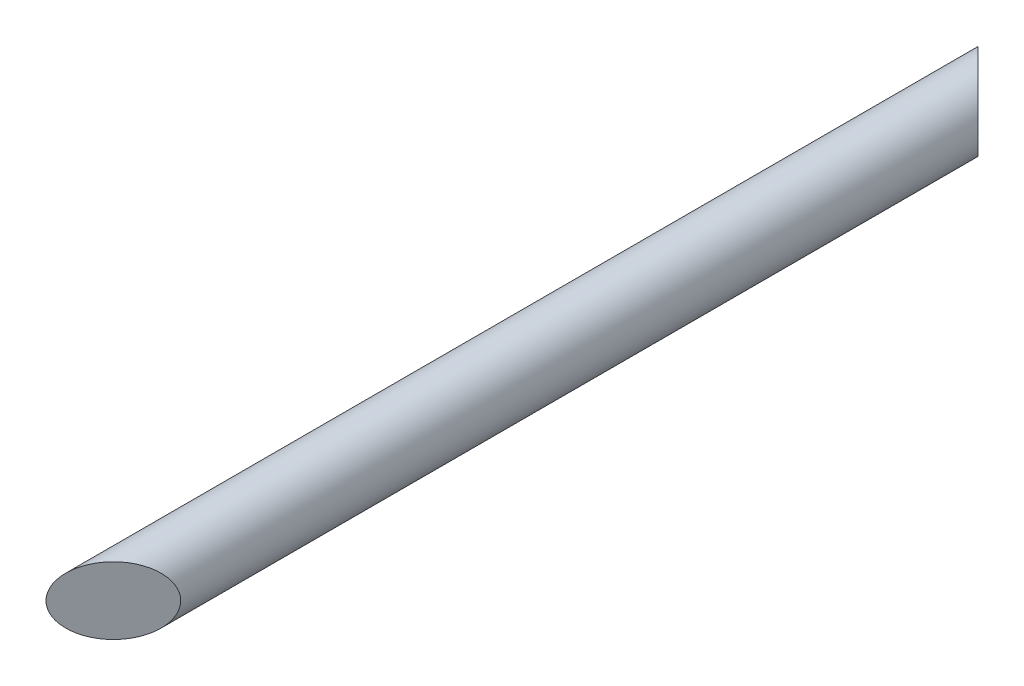
SolidWorks part; units mm, degrees
ref_plane "Front Plane" through (0, 0, 0) normal (0, 0, 1) x (1, 0, 0)
ref_plane "Top Plane" through (0, 0, 0) normal (0, 1, 0) x (1, 0, 0)
ref_plane "Right Plane" through (0, 0, 0) normal (1, 0, 0) x (0, 0, -1)
sketch "Sketch1" plane through (0, 0, 0) normal (0, 0, 1) x (1, 0, 0)
  circle A0 centre (0, 0) radius 30
  dimension "D1" = 60
extrude "Boss-Extrude2" add sketch "Sketch1" along normal blind 830 contours A0
ref_plane "Plane1" through (0, 40, 0) normal (0, 1, 0) x (1, 0, 0)
sketch "Sketch3" plane through (0, 40, 0) normal (0, 1, 0) x (1, 0, 0)
  line L0 (-30, 0) -> (30, -60)
  line L1 (30, -830) -> (30, 0) construction
  line L2 (30, -60) -> (30, 0)
  line L3 (30, 0) -> (-30, 0)
  dimension "D1" = 60
  dimension "D2" = 60
sketch "Sketch4" plane through (0, 40, 0) normal (0, 1, 0) x (1, 0, 0)
  line L0 (-30, -830) -> (30, -830)
  line L1 (30, -830) -> (30, -770)
  line L2 (30, -830) -> (30, 0) construction
  line L3 (30, -770) -> (-30, -830)
  point P4 (39.9956, -792.8601)
  dimension "D1" = 60
extrude "Cut-Extrude4" cut sketch "Sketch3" against normal blind 70
extrude "Cut-Extrude5" cut sketch "Sketch4" against normal blind 70
